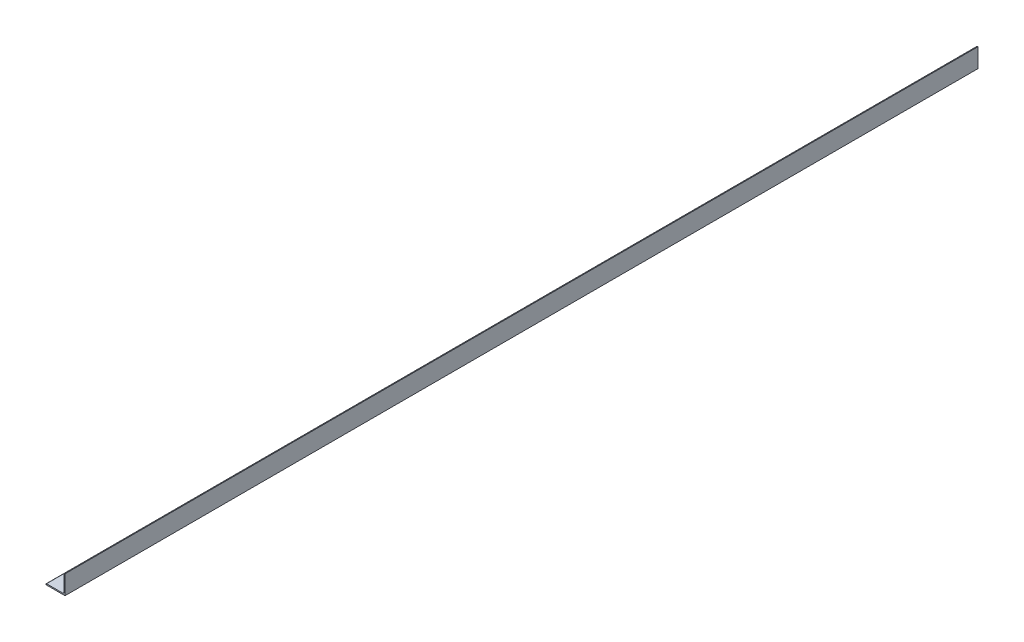
SolidWorks part; units mm, degrees
ref_plane "Front Plane" through (0, 0, 0) normal (0, 0, 1) x (1, 0, 0)
ref_plane "Top Plane" through (0, 0, 0) normal (0, 1, 0) x (1, 0, 0)
ref_plane "Right Plane" through (0, 0, 0) normal (1, 0, 0) x (0, 0, -1)
sketch "Sketch0" plane through (0, 0, 0) normal (0, 0, 1) x (1, 0, 0)
  line L0 (-12.7, -12.7) -> (12.7, -12.7)
  line L1 (12.7, -12.7) -> (12.7, 12.7)
  line L2 (12.7, 0) -> (0, 0) construction
  line L3 (0, 0) -> (0, -12.7) construction
  line L4 (11.1125, -9.5377) -> (11.1125, 12.7) construction
  line L5 (9.5377, -11.1125) -> (-12.7, -11.1125) construction
  arc A0 (11.1125, -9.5377) -> (9.5377, -11.1125) centre (9.5377, -9.5377) cw
  point P3 (10.6513, -10.6513)
  dimension "Inside Corner Radius" = 1.5748
  dimension "Outside Height" = 25.4
  dimension "Inside Height" = 23.8125
  dimension "Inside Width" = 23.8125
  dimension "Wall Thickness" = 1.5875
  dimension "D1" = 1.5875
  dimension "Outside Width" = 25.4
sketch "Sketch1" plane through (0, 0, 0) normal (1, 0, 0) x (0, 0, -1)
  line L0 (609.6, 0) -> (-609.6, 0)
  point P4 (0, 0)
  dimension "Length" = 1219.2
sketch "Sketch2" plane through (0, 0, 0) normal (0, 0, 1) x (1, 0, 0)
  line L0 (-12.7, -12.7) -> (12.7, -12.7)
  line L1 (12.7, -12.7) -> (12.7, 12.7)
  line L2 (12.7, 12.7) -> (11.1125, 12.7) construction
  line L3 (11.1125, 11.9062) -> (11.1125, -9.5377)
  line L4 (9.5377, -11.1125) -> (-11.9062, -11.1125)
  line L5 (-12.7, -12.7) -> (-12.7, -11.1125) construction
  line L6 (11.9062, 12.7) -> (12.7, 12.7)
  line L7 (-12.7, -11.9062) -> (-12.7, -12.7)
  line L8 (12.7, 0) -> (0, 0) construction
  line L9 (0, 0) -> (0, -12.7) construction
  arc A0 (11.1125, 11.9062) -> (11.9062, 12.7) centre (11.9062, 11.9062) cw
  arc A1 (-12.7, -11.9062) -> (-11.9062, -11.1125) centre (-11.9062, -11.9062) cw
  arc A2 (11.1125, -9.5377) -> (9.5377, -11.1125) centre (9.5377, -9.5377) cw
  dimension "Inside Radius" = 1.5748
  dimension "Height" = 25.4
  dimension "Width" = 25.4
  dimension "Thickness" = 1.5875
extrude "Boss-Extrude1" add sketch "Sketch2" along normal mid plane 1219.2
sketch "Break Locations" plane through (0, 0, 0) normal (1, 0, 0) x (0, 0, -1)
  line L0 (-583.692, 0) -> (583.692, 0)
  line L1 (-609.6, -12.7) -> (-609.6, 12.7) construction
  line L2 (609.6, -12.7) -> (609.6, 12.7) construction
  point P0 (-588.01, 0)
  point P1 (588.01, 0)
  point P10 (0, 0)
  point P11 (583.692, 0)
  point P13 (-583.692, 0)
  dimension "D1" = 21.59
  dimension "D2" = 21.59
  dimension "D3" = 25.908
equation "\"D1@Break Locations\" = .85 * \"Height@Sketch2\""
equation "\"D2@Break Locations\"=\"D1@Break Locations\""
equation "\"Thickness@Sketch2\"=\"wall thickness@sketch0\""
equation "\"Height@Sketch2\"=\"outside height@sketch0\""
equation "\"Width@Sketch2\"=\"outside width@sketch0\""
equation "\"Inside Radius@Sketch2\"=\"inside corner radius@sketch0\""
equation "\"Length@Boss-Extrude1\"=\"length@sketch1\""
equation "\"D3@Break Locations\"=\"D2@Break Locations\"*1.2"
equation "\"D1@Sketch0\"=\"Wall Thickness@Sketch0\""
